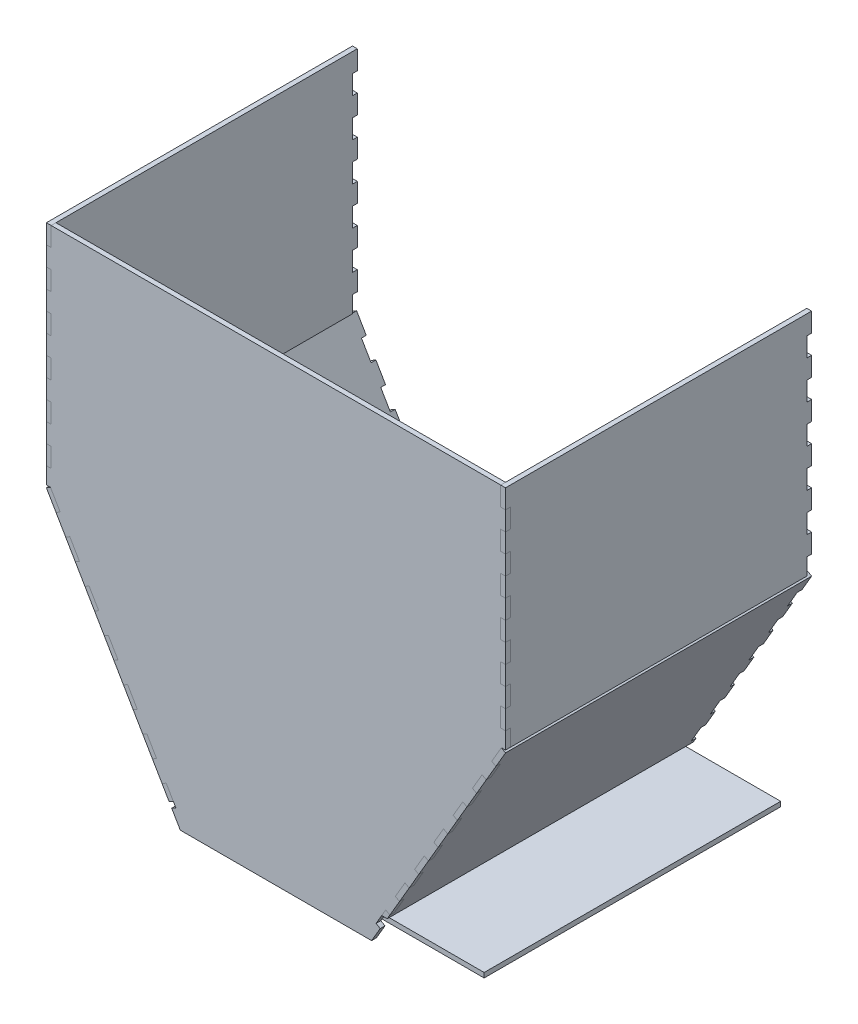
SolidWorks part; units mm, degrees
ref_plane "Front Plane" through (0, 0, 0) normal (0, 0, 1) x (1, 0, 0)
ref_plane "Top Plane" through (0, 0, 0) normal (0, 1, 0) x (1, 0, 0)
ref_plane "Right Plane" through (0, 0, 0) normal (1, 0, 0) x (0, 0, -1)
sketch "Sketch1" plane through (0, 0, 0) normal (0, 0, 1) x (1, 0, 0)
  line L0 (-152.4, -76.2) -> (-63.5, -228.6)
  line L1 (152.4, -76.2) -> (-152.4, -76.2)
  line L2 (152.4, -76.2) -> (152.4, 76.2)
  line L3 (152.4, 76.2) -> (-152.4, 76.2)
  line L4 (-152.4, -76.2) -> (-152.4, 76.2)
  line L5 (152.4, -76.2) -> (-152.4, 76.2) construction
  line L6 (152.4, 76.2) -> (-152.4, -76.2) construction
  line L7 (-63.5, -228.6) -> (63.5, -228.6)
  line L8 (63.5, -228.6) -> (152.4, -76.2)
  point P0 (0, 0)
  dimension "D1" = 152.4
  dimension "D2" = 304.8
  dimension "D3" = 152.4
  dimension "D4" = 127
extrude "Boss-Extrude1" add sketch "Sketch1" along normal blind 3.175 contours L4 L1 L2 L3 | L7 L8 L1 L0
sketch "Sketch2" plane through (0, 0, 3.175) normal (0, 0, 1) x (1, 0, 0)
  line L0 (-152.4, 38.1) -> (-149.225, 38.1)
  line L1 (-152.4, 76.2) -> (-149.225, 76.2)
  line L2 (-152.4, 76.2) -> (-152.4, 63.5)
  line L3 (-152.4, 63.5) -> (-149.225, 63.5)
  line L4 (-149.225, 76.2) -> (-149.225, 63.5)
  line L5 (-149.225, 50.8) -> (-149.225, 38.1)
  line L6 (-152.4, 50.8) -> (-149.225, 50.8)
  line L7 (-152.4, 12.7) -> (-149.225, 12.7)
  line L8 (-149.225, 25.4) -> (-149.225, 12.7)
  line L9 (-152.4, 25.4) -> (-149.225, 25.4)
  line L10 (-152.4, -12.7) -> (-149.225, -12.7)
  line L11 (-149.225, 0) -> (-149.225, -12.7)
  line L12 (-152.4, 0) -> (-149.225, 0)
  line L13 (-152.4, -38.1) -> (-149.225, -38.1)
  line L14 (-149.225, -25.4) -> (-149.225, -38.1)
  line L15 (-152.4, -25.4) -> (-149.225, -25.4)
  line L16 (-152.4, -63.5) -> (-149.225, -63.5)
  line L17 (-149.225, -50.8) -> (-149.225, -63.5)
  line L18 (-152.4, -50.8) -> (-149.225, -50.8)
  line L19 (-152.4, 63.5) -> (-152.4, 38.1) construction
  line L20 (0, 0) -> (0, 76.2) construction
  line L21 (152.4, 76.2) -> (-152.4, 76.2) construction
  line L22 (152.4, 63.5) -> (152.4, 38.1) construction
  line L23 (152.4, -50.8) -> (149.225, -50.8)
  line L24 (149.225, -50.8) -> (149.225, -63.5)
  line L25 (152.4, -63.5) -> (149.225, -63.5)
  line L26 (152.4, -25.4) -> (149.225, -25.4)
  line L27 (149.225, -25.4) -> (149.225, -38.1)
  line L28 (152.4, -38.1) -> (149.225, -38.1)
  line L29 (152.4, 0) -> (149.225, 0)
  line L30 (149.225, 0) -> (149.225, -12.7)
  line L31 (152.4, -12.7) -> (149.225, -12.7)
  line L32 (152.4, 25.4) -> (149.225, 25.4)
  line L33 (149.225, 25.4) -> (149.225, 12.7)
  line L34 (152.4, 12.7) -> (149.225, 12.7)
  line L35 (152.4, 50.8) -> (149.225, 50.8)
  line L36 (149.225, 50.8) -> (149.225, 38.1)
  line L37 (149.225, 76.2) -> (149.225, 63.5)
  line L38 (152.4, 63.5) -> (149.225, 63.5)
  line L39 (152.4, 76.2) -> (152.4, 63.5)
  line L40 (152.4, 76.2) -> (149.225, 76.2)
  line L41 (152.4, 38.1) -> (149.225, 38.1)
  line L42 (-152.4, -76.2) -> (-146.0008, -87.17)
  line L43 (-152.4, -76.2) -> (-149.6575, -74.6002)
  line L44 (-146.0008, -87.17) -> (-143.2583, -85.5702)
  line L45 (-149.6575, -74.6002) -> (-143.2583, -85.5702)
  line L46 (-152.4, -76.2) -> (-63.5, -228.6) construction
  line L47 (-136.8592, -96.5402) -> (-130.46, -107.5102)
  line L48 (-139.6017, -98.14) -> (-136.8592, -96.5402)
  line L49 (-133.2025, -109.11) -> (-130.46, -107.5102)
  line L50 (-124.0609, -118.4802) -> (-117.6617, -129.4502)
  line L51 (-126.8034, -120.08) -> (-124.0609, -118.4802)
  line L52 (-120.4042, -131.05) -> (-117.6617, -129.4502)
  line L53 (-111.2625, -140.4202) -> (-104.8634, -151.3902)
  line L54 (-114.005, -142.02) -> (-111.2625, -140.4202)
  line L55 (-107.6059, -152.9899) -> (-104.8634, -151.3902)
  line L56 (-98.4642, -162.3601) -> (-92.065, -173.3301)
  line L57 (-101.2067, -163.9599) -> (-98.4642, -162.3601)
  line L58 (-94.8075, -174.9299) -> (-92.065, -173.3301)
  line L59 (-85.6659, -184.3001) -> (-79.2667, -195.2701)
  line L60 (-88.4084, -185.8999) -> (-85.6659, -184.3001)
  line L61 (-82.0092, -196.8699) -> (-79.2667, -195.2701)
  line L62 (-72.8676, -206.2401) -> (-66.4684, -217.2101)
  line L63 (-75.6101, -207.8399) -> (-72.8676, -206.2401)
  line L64 (-69.2109, -218.8099) -> (-66.4684, -217.2101)
  line L65 (149.6575, -74.6002) -> (143.2583, -85.5702)
  line L67 (69.2109, -218.8099) -> (66.4684, -217.2101)
  line L68 (75.6101, -207.8399) -> (72.8676, -206.2401)
  line L69 (72.8676, -206.2401) -> (66.4684, -217.2101)
  line L70 (82.0092, -196.8699) -> (79.2667, -195.2701)
  line L71 (88.4084, -185.8999) -> (85.6659, -184.3001)
  line L72 (85.6659, -184.3001) -> (79.2667, -195.2701)
  line L73 (94.8075, -174.9299) -> (92.065, -173.3301)
  line L74 (101.2067, -163.9599) -> (98.4642, -162.3601)
  line L75 (98.4642, -162.3601) -> (92.065, -173.3301)
  line L76 (107.6059, -152.9899) -> (104.8634, -151.3902)
  line L77 (114.005, -142.02) -> (111.2625, -140.4202)
  line L78 (111.2625, -140.4202) -> (104.8634, -151.3902)
  line L79 (120.4042, -131.05) -> (117.6617, -129.4502)
  line L80 (126.8034, -120.08) -> (124.0609, -118.4802)
  line L81 (124.0609, -118.4802) -> (117.6617, -129.4502)
  line L82 (133.2025, -109.11) -> (130.46, -107.5102)
  line L83 (139.6017, -98.14) -> (136.8592, -96.5402)
  line L84 (136.8592, -96.5402) -> (130.46, -107.5102)
  line L85 (146.0008, -87.17) -> (143.2583, -85.5702)
  line L86 (152.4, -76.2) -> (146.0008, -87.17)
  line L87 (-149.6575, -74.6002) -> (-152.4, -74.6002)
  line L88 (-152.4, -76.2) -> (-152.4, 76.2) construction
  line L89 (149.6575, -74.6002) -> (152.4, -74.6002)
  line L90 (152.4, -76.2) -> (152.4, 76.2) construction
  line M27 (-152.4, 76.2) -> (-152.4, -76.2)
  line M28 (-152.4, -76.2) -> (-63.5, -228.6)
  line M30 (63.5, -228.6) -> (152.4, -76.2)
  line M31 (152.4, -76.2) -> (152.4, 76.2)
  line M32 (152.4, 76.2) -> (-152.4, 76.2)
  dimension "D1" = 3.175
  dimension "D2" = 12.7
  dimension "D4" = 25.4
  dimension "D6" = 10.97
  dimension "D3" = 6
  dimension "D5" = 7
extrude "Cut-Extrude1" cut sketch "Sketch2" against normal blind 3.175 contours L4 L3 M32 M27 | L6 L0 L5 M27 | L9 L7 L8 M27 | L12 L10 L11 M27 | L15 L13 L14 M27 | L18 L16 L17 M27 | L45 L43 L44 M28 | L49 L47 L48 M28 | L52 L50 L51 M28 | L55 L53 L54 M28 | L58 L56 L57 M28 | L61 L59 L60 M28 | L64 L62 L63 M28 | L68 L69 L67 M30 | L71 L72 L70 M30 | L74 L75 L73 M30 | L77 L78 L76 M30 | L80 L81 L79 M30 | L83 L84 L82 M30 | L25 L23 L24 M31 | L28 L26 L27 M31 | L31 L29 L30 M31 | L34 L32 L33 M31 | L41 L35 L36 M31 | L38 L37 M31 M32 | L43 L87 M27 | L89 L65 L85 M30 M31
sketch "Sketch3" plane through (-149.225, 0, 0) normal (-1, 0, 0) x (0, 0, 1)
  line L0 (3.175, -63.5) -> (0, -63.5) construction
  line L1 (3.175, 76.2) -> (-200.025, 76.2)
  line L2 (3.175, 76.2) -> (3.175, -76.2)
  line L3 (3.175, -76.2) -> (-200.025, -76.2)
  line L4 (-200.025, 76.2) -> (-200.025, -76.2)
  line L5 (0, -63.5) -> (0, -74.6002) construction
  line L6 (0, -74.6002) -> (3.175, -74.6002) construction
  line L7 (3.175, -74.6002) -> (3.175, -63.5) construction
  line L8 (3.175, -38.1) -> (0, -38.1) construction
  line L9 (0, -38.1) -> (0, -50.8) construction
  line L10 (0, -50.8) -> (3.175, -50.8) construction
  line L11 (3.175, -50.8) -> (3.175, -38.1) construction
  line L12 (3.175, -12.7) -> (0, -12.7) construction
  line L13 (0, -12.7) -> (0, -25.4) construction
  line L14 (0, -25.4) -> (3.175, -25.4) construction
  line L15 (3.175, -25.4) -> (3.175, -12.7) construction
  line L16 (3.175, 12.7) -> (0, 12.7) construction
  line L17 (0, 12.7) -> (0, 0) construction
  line L18 (0, 0) -> (3.175, 0) construction
  line L19 (3.175, 0) -> (3.175, 12.7) construction
  line L20 (3.175, 38.1) -> (0, 38.1) construction
  line L21 (0, 38.1) -> (0, 25.4) construction
  line L22 (0, 25.4) -> (3.175, 25.4) construction
  line L23 (3.175, 25.4) -> (3.175, 38.1) construction
  line L24 (0, 63.5) -> (0, 50.8) construction
  line L25 (0, 50.8) -> (3.175, 50.8) construction
  line L26 (3.175, 50.8) -> (3.175, 63.5) construction
  line L27 (3.175, 63.5) -> (0, 63.5) construction
  line L28 (3.175, -63.5) -> (0, -63.5)
  line L29 (0, -63.5) -> (0, -74.6002)
  line L30 (0, -74.6002) -> (3.175, -74.6002)
  line L31 (3.175, -74.6002) -> (3.175, -63.5)
  line L32 (3.175, -38.1) -> (0, -38.1)
  line L33 (0, -38.1) -> (0, -50.8)
  line L34 (0, -50.8) -> (3.175, -50.8)
  line L35 (3.175, -50.8) -> (3.175, -38.1)
  line L36 (3.175, -12.7) -> (0, -12.7)
  line L37 (0, -12.7) -> (0, -25.4)
  line L38 (0, -25.4) -> (3.175, -25.4)
  line L39 (3.175, -25.4) -> (3.175, -12.7)
  line L40 (3.175, 12.7) -> (0, 12.7)
  line L41 (0, 12.7) -> (0, 0)
  line L42 (0, 0) -> (3.175, 0)
  line L43 (3.175, 0) -> (3.175, 12.7)
  line L44 (3.175, 38.1) -> (0, 38.1)
  line L45 (0, 38.1) -> (0, 25.4)
  line L46 (0, 25.4) -> (3.175, 25.4)
  line L47 (3.175, 25.4) -> (3.175, 38.1)
  line L48 (0, 63.5) -> (0, 50.8)
  line L49 (0, 50.8) -> (3.175, 50.8)
  line L50 (3.175, 50.8) -> (3.175, 63.5)
  line L51 (3.175, 63.5) -> (0, 63.5)
  line L52 (0, -74.6002) -> (-200.025, -74.6002)
  line L53 (-98.425, 76.2) -> (-98.425, -74.6002) construction
  line L54 (-200.025, 63.5) -> (-196.85, 63.5)
  line L55 (-200.025, 50.8) -> (-200.025, 63.5)
  line L56 (-196.85, 50.8) -> (-200.025, 50.8)
  line L57 (-196.85, 63.5) -> (-196.85, 50.8)
  line L58 (-200.025, 25.4) -> (-200.025, 38.1)
  line L59 (-196.85, 25.4) -> (-200.025, 25.4)
  line L60 (-196.85, 38.1) -> (-196.85, 25.4)
  line L61 (-200.025, 38.1) -> (-196.85, 38.1)
  line L62 (-200.025, 0) -> (-200.025, 12.7)
  line L63 (-196.85, 0) -> (-200.025, 0)
  line L64 (-196.85, 12.7) -> (-196.85, 0)
  line L65 (-200.025, 12.7) -> (-196.85, 12.7)
  line L66 (-200.025, -25.4) -> (-200.025, -12.7)
  line L67 (-196.85, -25.4) -> (-200.025, -25.4)
  line L68 (-196.85, -12.7) -> (-196.85, -25.4)
  line L69 (-200.025, -12.7) -> (-196.85, -12.7)
  line L70 (-200.025, -50.8) -> (-200.025, -38.1)
  line L71 (-196.85, -50.8) -> (-200.025, -50.8)
  line L72 (-196.85, -38.1) -> (-196.85, -50.8)
  line L73 (-200.025, -38.1) -> (-196.85, -38.1)
  line L74 (-200.025, -74.6002) -> (-200.025, -63.5)
  line L75 (-196.85, -74.6002) -> (-200.025, -74.6002)
  line L76 (-196.85, -63.5) -> (-196.85, -74.6002)
  line L77 (-200.025, -63.5) -> (-196.85, -63.5)
  line M4 (3.175, 63.5) -> (3.175, 76.2)
  line M5 (3.175, 76.2) -> (0, 76.2)
  line M6 (0, 76.2) -> (0, 63.5)
  line M7 (0, 63.5) -> (3.175, 63.5)
  dimension "D1" = 203.2
  dimension "D2" = 152.4
extrude "Boss-Extrude2" add sketch "Sketch3" along normal blind 3.175 separate body contours L53 L1 L4 L54 L57 L56 L61 L60 L59 L65 L64 L63 L69 L68 L67 L73 L72 L71 L77 L76 L52 | L1 L53 L52 L29 L28 L2 L34 L33 L32 L38 L37 L36 L42 L41 L40 L46 L45 L44 L49 L48 M6 | M7 M4 M5 M6
sketch "Sketch4" plane through (-144.13, -84.0759, 0) normal (-0.8638, -0.5039, 0) x (0, 0, 1)
  line L0 (3.175, -165.464) -> (3.175, -154.13) construction
  line L1 (3.175, 10.97) -> (-200.025, 10.97)
  line L2 (3.175, 10.97) -> (3.175, -165.464)
  line L3 (3.175, -165.464) -> (-200.025, -165.464)
  line L4 (-200.025, 10.97) -> (-200.025, -165.464)
  line L5 (3.175, -154.13) -> (0, -154.13) construction
  line L6 (0, -154.13) -> (0, -165.464) construction
  line L7 (0, -165.464) -> (3.175, -165.464) construction
  line L8 (3.175, -141.43) -> (3.175, -128.73) construction
  line L9 (3.175, -128.73) -> (0, -128.73) construction
  line L10 (0, -128.73) -> (0, -141.43) construction
  line L11 (0, -141.43) -> (3.175, -141.43) construction
  line L12 (3.175, -116.03) -> (3.175, -103.33) construction
  line L13 (3.175, -103.33) -> (0, -103.33) construction
  line L14 (0, -103.33) -> (0, -116.03) construction
  line L15 (0, -116.03) -> (3.175, -116.03) construction
  line L16 (3.175, -90.63) -> (3.175, -77.93) construction
  line L17 (3.175, -77.93) -> (0, -77.93) construction
  line L18 (0, -77.93) -> (0, -90.63) construction
  line L19 (0, -90.63) -> (3.175, -90.63) construction
  line L20 (3.175, -65.23) -> (3.175, -52.53) construction
  line L21 (3.175, -52.53) -> (0, -52.53) construction
  line L22 (0, -52.53) -> (0, -65.23) construction
  line L23 (0, -65.23) -> (3.175, -65.23) construction
  line L24 (3.175, -39.83) -> (3.175, -27.13) construction
  line L25 (3.175, -27.13) -> (0, -27.13) construction
  line L26 (0, -27.13) -> (0, -39.83) construction
  line L27 (0, -39.83) -> (3.175, -39.83) construction
  line L28 (0, -14.43) -> (3.175, -14.43) construction
  line L29 (3.175, -14.43) -> (3.175, -1.73) construction
  line L30 (3.175, -1.73) -> (0, -1.73) construction
  line L31 (0, -1.73) -> (0, -14.43) construction
  line L32 (3.175, -165.464) -> (3.175, -154.13)
  line L33 (3.175, -154.13) -> (0, -154.13)
  line L34 (0, -154.13) -> (0, -165.464)
  line L35 (0, -165.464) -> (3.175, -165.464)
  line L36 (3.175, -141.43) -> (3.175, -128.73)
  line L37 (3.175, -128.73) -> (0, -128.73)
  line L38 (0, -128.73) -> (0, -141.43)
  line L39 (0, -141.43) -> (3.175, -141.43)
  line L40 (3.175, -116.03) -> (3.175, -103.33)
  line L41 (3.175, -103.33) -> (0, -103.33)
  line L42 (0, -103.33) -> (0, -116.03)
  line L43 (0, -116.03) -> (3.175, -116.03)
  line L44 (3.175, -90.63) -> (3.175, -77.93)
  line L45 (3.175, -77.93) -> (0, -77.93)
  line L46 (0, -77.93) -> (0, -90.63)
  line L47 (0, -90.63) -> (3.175, -90.63)
  line L48 (3.175, -65.23) -> (3.175, -52.53)
  line L49 (3.175, -52.53) -> (0, -52.53)
  line L50 (0, -52.53) -> (0, -65.23)
  line L51 (0, -65.23) -> (3.175, -65.23)
  line L52 (3.175, -39.83) -> (3.175, -27.13)
  line L53 (3.175, -27.13) -> (0, -27.13)
  line L54 (0, -27.13) -> (0, -39.83)
  line L55 (0, -39.83) -> (3.175, -39.83)
  line L56 (0, -14.43) -> (3.175, -14.43)
  line L57 (3.175, -14.43) -> (3.175, -1.73)
  line L58 (3.175, -1.73) -> (0, -1.73)
  line L59 (0, -1.73) -> (0, -14.43)
  line L60 (-98.425, 10.97) -> (-98.425, -165.464) construction
  line L61 (-196.85, -1.73) -> (-196.85, -14.43)
  line L62 (-200.025, -1.73) -> (-196.85, -1.73)
  line L63 (-200.025, -14.43) -> (-200.025, -1.73)
  line L64 (-196.85, -14.43) -> (-200.025, -14.43)
  line L65 (-196.85, -39.83) -> (-200.025, -39.83)
  line L66 (-196.85, -27.13) -> (-196.85, -39.83)
  line L67 (-200.025, -27.13) -> (-196.85, -27.13)
  line L68 (-200.025, -39.83) -> (-200.025, -27.13)
  line L69 (-196.85, -65.23) -> (-200.025, -65.23)
  line L70 (-196.85, -52.53) -> (-196.85, -65.23)
  line L71 (-200.025, -52.53) -> (-196.85, -52.53)
  line L72 (-200.025, -65.23) -> (-200.025, -52.53)
  line L73 (-196.85, -90.63) -> (-200.025, -90.63)
  line L74 (-196.85, -77.93) -> (-196.85, -90.63)
  line L75 (-200.025, -77.93) -> (-196.85, -77.93)
  line L76 (-200.025, -90.63) -> (-200.025, -77.93)
  line L77 (-196.85, -116.03) -> (-200.025, -116.03)
  line L78 (-200.025, -116.03) -> (-200.025, -103.33)
  line L79 (-196.85, -141.43) -> (-200.025, -141.43)
  line L80 (-196.85, -128.73) -> (-196.85, -141.43)
  line L81 (-200.025, -128.73) -> (-196.85, -128.73)
  line L82 (-200.025, -141.43) -> (-200.025, -128.73)
  line L83 (-196.85, -165.464) -> (-200.025, -165.464)
  line L84 (-196.85, -154.13) -> (-196.85, -165.464)
  line L85 (-200.025, -154.13) -> (-196.85, -154.13)
  line L86 (-200.025, -165.464) -> (-200.025, -154.13)
  line L87 (-196.85, -103.33) -> (-196.85, -116.03)
  line L88 (-200.025, -103.33) -> (-196.85, -103.33)
  line M3 (3.175, -1.73) -> (3.175, 10.97)
  line M4 (3.175, 10.97) -> (0, 10.97)
  line M5 (0, 10.97) -> (0, -1.73)
  line M6 (0, -1.73) -> (3.175, -1.73)
  dimension "D1" = 203.2
extrude "Boss-Extrude3" add sketch "Sketch4" along normal blind 3.175 separate body contours L60 L1 L4 L62 L61 L64 L67 L66 L65 L71 L70 L69 L75 L74 L73 L88 L87 L77 L81 L80 L79 L85 L84 L3 | L1 L60 L3 L34 L33 L2 L39 L38 L37 L43 L42 L41 L47 L46 L45 L51 L50 L49 L55 L54 L53 L56 L59 M5 | M6 M3 M4 M5
sketch "Sketch5" plane through (0, 0, 0) normal (0, 0, -1) x (-1, 0, 0)
  line L0 (70.9083, -215.9) -> (68.1658, -214.3002)
  line L1 (-127.0129, -228.6) -> (120.2705, -228.6)
  line L2 (-127.0129, -228.6) -> (-127.0129, -215.9)
  line L3 (-127.0129, -215.9) -> (67.2326, -215.9)
  line L4 (120.2705, -228.6) -> (120.2705, -215.9)
  line L5 (75.6101, -207.8399) -> (69.2109, -218.8099) construction
  line L6 (72.8676, -206.2401) -> (66.4684, -217.2101) construction
  line L7 (68.1658, -214.3002) -> (67.2326, -215.9)
  line L8 (70.9083, -215.9) -> (120.2705, -215.9)
  dimension "D1" = 12.7
extrude "Cut-Extrude2" cut sketch "Sketch5" along normal blind 965.327 and the other way blind 965.327
mirror "Mirror1" about plane through (0, 0, 0) normal (1, 0, 0) of bodies 105 107
sketch "Sketch6" plane through (0, 0, -200.025) normal (0, 0, -1) x (-1, 0, 0)
  line L0 (-70.196, -210.82) -> (-73.8717, -210.82)
  line L1 (-72.8676, -206.2401) -> (-68.1658, -214.3002) construction
  line L2 (-75.6101, -207.8399) -> (-70.9083, -215.9) construction
  line L7 (-68.1658, -214.3002) -> (-72.8676, -206.2401)
  line L8 (-72.8676, -206.2401) -> (-75.6101, -207.8399)
  line L9 (-75.6101, -207.8399) -> (-70.9083, -215.9)
  line L10 (-70.9083, -215.9) -> (-68.1658, -214.3002)
  line L11 (-68.1658, -214.3002) -> (-72.8676, -206.2401)
  line L12 (-72.8676, -206.2401) -> (-75.6101, -207.8399)
  line L13 (-75.6101, -207.8399) -> (-70.9083, -215.9)
  line L14 (-70.9083, -215.9) -> (-68.1658, -214.3002)
  line M6 (-68.1658, -214.3002) -> (-72.8676, -206.2401)
  line M8 (-75.6101, -207.8399) -> (-70.9083, -215.9)
  line M9 (-70.9083, -215.9) -> (-68.1658, -214.3002)
  dimension "D1" = 17.78
  dimension "D2" = 0
extrude "Cut-Extrude3" cut sketch "Sketch6" against normal blind 965.327 contours L0 M6 M8 M9
sketch "Sketch7" plane through (0, 0, 0) normal (0, 0, -1) x (-1, 0, 0)
  line L1 (70.9083, -228.6) -> (-183.0917, -228.6)
  line L2 (70.9083, -228.6) -> (70.9083, -215.9)
  line L3 (70.9083, -215.9) -> (-183.0917, -215.9)
  line L4 (-183.0917, -228.6) -> (-183.0917, -215.9)
  line L5 (-135.0342, -215.9) -> (68.1658, -215.9)
  line L6 (-135.0342, -215.9) -> (-135.0342, -212.725)
  line L7 (-135.0342, -212.725) -> (68.1658, -212.725)
  line L8 (68.1658, -215.9) -> (68.1658, -212.725)
  dimension "D1" = 12.7
  dimension "D2" = 254
  dimension "D3" = 3.175
  dimension "D4" = 203.2
extrude "Boss-Extrude4" add sketch "Sketch7" along normal blind 196.85 separate body contours L3 L8 L7 L6
